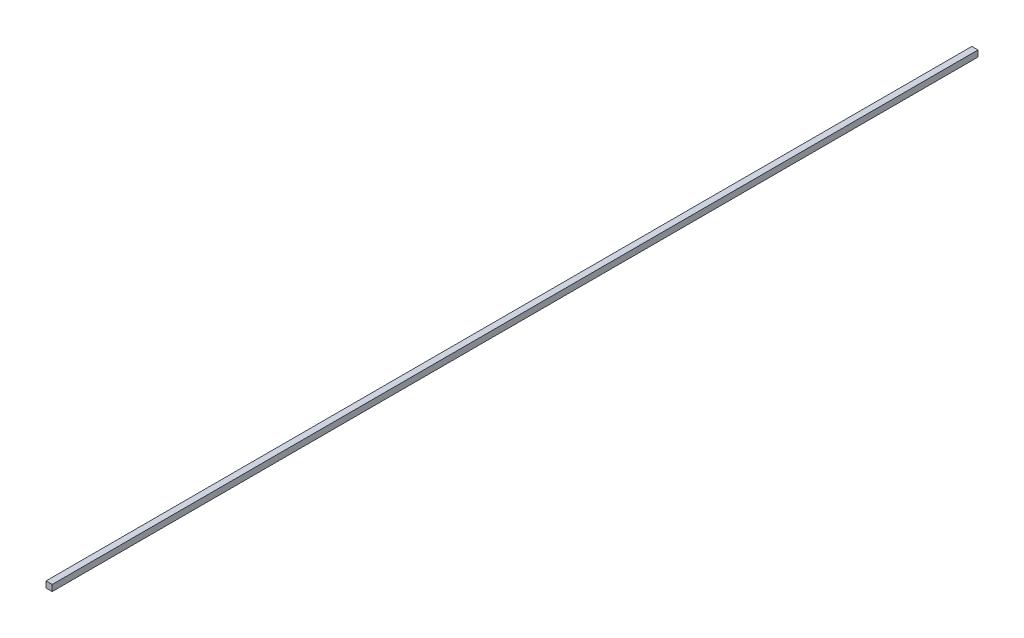
SolidWorks part; units mm, degrees
material "ﾊﾞﾙｻ"
ref_plane "正面" through (0, 0, 0) normal (0, 0, 1) x (1, 0, 0)
ref_plane "平面" through (0, 0, 0) normal (0, 1, 0) x (1, 0, 0)
ref_plane "右側面" through (0, 0, 0) normal (1, 0, 0) x (0, 0, -1)
sketch "ｽｹｯﾁ1" plane through (0, 0, 0) normal (0, 0, 1) x (1, 0, 0)
  line L1 (-2, 2) -> (2, 2)
  line L2 (-2, 2) -> (-2, -2)
  line L3 (-2, -2) -> (2, -2)
  line L4 (2, 2) -> (2, -2)
  line L5 (-2, 2) -> (2, -2) construction
  line L6 (-2, -2) -> (2, 2) construction
  point P0 (0, 0)
  dimension "D1" = 4
  dimension "D2" = 4
extrude "ﾎﾞｽ - 押し出し1" add sketch "ｽｹｯﾁ1" along normal blind 600
